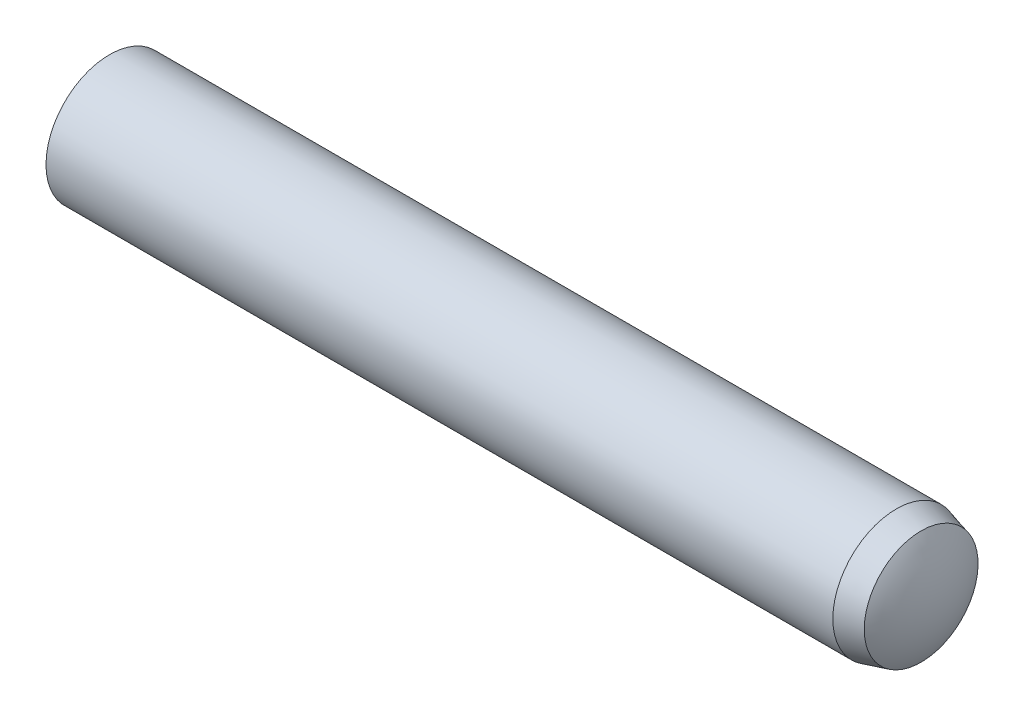
SolidWorks part; units mm, degrees
ref_plane "Front Plane" through (0, 0, 0) normal (0, 0, 1) x (1, 0, 0)
ref_plane "Top Plane" through (0, 0, 0) normal (0, 1, 0) x (1, 0, 0)
ref_plane "Right Plane" through (0, 0, 0) normal (1, 0, 0) x (0, 0, -1)
sketch "Sketch1" plane through (0, 0, 0) normal (0, 0, 1) x (1, 0, 0)
  line L0 (-20, 0) -> (20, 0) construction
  line L1 (20, 3) -> (20, -3) construction
  line L2 (-20, 3) -> (-20, -3) construction
  line L3 (18.05, 3) -> (18.05, -3) construction
  line L4 (-19.1, 3) -> (-19.1, -3) construction
  line L5 (-20, 0) -> (-19.1, 0) construction
  line L6 (20, 0) -> (18.05, 0) construction
  line L7 (19.22, 3) -> (19.22, -3) construction
  dimension "D1" = 1.95
  dimension "Dia" = 6
  dimension "D2" = 0.9
  dimension "Length" = 40
  dimension "D3" = 1.17
sketch "Sketch2" plane through (0, 0, 0) normal (1, 0, 0) x (0, 0, -1)
  circle A0 centre (0, 0) radius 3
extrude "Extrude1" add sketch "Sketch2" against normal up to vertex (20 mm away) and the other way up to vertex (20 mm away) up to point (-20, 0, 0) other way up to point (20, 0, 0)
sketch "Sketch5" plane through (0, 0, 0) normal (0, 0, 1) x (1, 0, 0)
  line L0 (18.05, 3) -> (18.05, 3.5)
  line L1 (18.05, 3.5) -> (20.5, 3.5)
  line L2 (20.5, 3.5) -> (20.5, 0)
  line L3 (20, 0) -> (20.5, 0)
  line L5 (-19.1, 3) -> (-19.1, 3.5)
  line L6 (-19.1, 3.5) -> (-20.5, 3.5)
  line L7 (-20.5, 3.5) -> (-20.5, 0)
  line L8 (18.05, 3) -> (19.22, 2.6865)
  line L10 (-20, 0) -> (-20.5, 0)
  line L11 (-20, 3) -> (-20, -3) construction
  line L13 (18.05, 3) -> (18.05, -3) construction
  line L15 (-20, 0) -> (20, 0) construction
  line L16 (19.22, 3) -> (19.22, -3) construction
  line L17 (20, 3) -> (20, -3) construction
  arc A0 (19.22, 2.6865) -> (20, 0) centre (14.9835, 0) cw
  arc A1 (-19.1, 3) -> (-20, 0) centre (-14.55, 0) ccw
  dimension "D1" = 15
  dimension "D2" = 0.5
revolve "Cut-Revolve1" cut sketch "Sketch5" angle 360 about L0
equation "\"D1@Sketch1\" = \"Dia@Sketch1\"*.325"
equation "\"D2@Sketch1\" = \"Dia@Sketch1\"*.15"
equation "\"D3@Sketch1\" = \"D1@Sketch1\"*.6"
